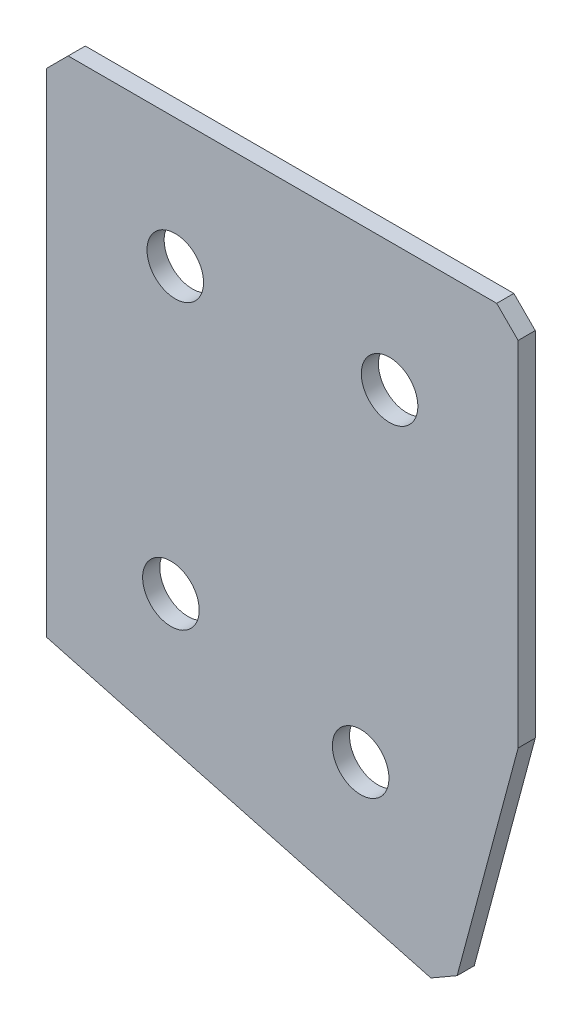
SolidWorks part; units mm, degrees
material "Простая углеродистая сталь"
ref_plane "Спереди" through (0, 0, 0) normal (0, 0, 1) x (1, 0, 0)
ref_plane "Сверху" through (0, 0, 0) normal (0, 1, 0) x (1, 0, 0)
ref_plane "Справа" through (0, 0, 0) normal (1, 0, 0) x (0, 0, -1)
sketch "Эскиз3" plane through (0, 0, 0) normal (0, 0, -1) x (1, 0, 0)
  line L0 (0, 0) -> (55, 0)
  line L1 (55, 0) -> (55, 43.6789)
  line L2 (0, 0) -> (0, 60)
  line L3 (0, 60) -> (47.2354, 72.6567)
  line L4 (47.2354, 72.6567) -> (55, 43.6789)
  dimension "D1" = 55
  dimension "D2" = 60
  dimension "D3" = 30
  dimension "D4" = 15
  dimension "D5" = 43.6789
extrude "Бобышка-Вытянуть1" add sketch "Эскиз3" along normal blind 2
hole_wizard "Отверстие с зазором M61" positions "Эскиз4" profile "Эскиз5" hole size "M6" standard "DIN" end condition through all
sketch "Эскиз4" plane through (0, 0, -2) normal (0, 0, -1) x (1, 0, 0)
  line L0 (14.4889, 48.3531) -> (36.6288, 54.2855) construction
  line L2 (47.2354, 72.6567) -> (0, 60) construction
  line L3 (15, 15) -> (40, 15) construction
  line L5 (0, 0) -> (55, 0) construction
  line L6 (0, 60) -> (0, 0) construction
  line L7 (55, 0) -> (55, 43.6789) construction
  line L8 (55, 43.6789) -> (47.2354, 72.6567) construction
  line L9 (14.4889, 48.3531) -> (0, 44.4709) construction
  point P0 (15, 15)
  point P2 (40, 15)
  point P4 (14.4889, 48.3531)
  point P6 (36.6288, 54.2855)
  dimension "D1" = 15
  dimension "D2" = 15
  dimension "D3" = 15
  dimension "D4" = 15
  dimension "D5" = 15
  dimension "D6" = 15
  dimension "D7" = 22.921
  dimension "D8" = 25
sketch "Эскиз5" plane through (15, -15, -2) normal (1, 0, 0) x (0, 1, 0)
  line L0 (0, 0) -> (0, 2)
  line L1 (0, 2) -> (3.3, 2)
  line L2 (3.3, 2) -> (3.3, 0)
  line L5 (3.3, 0) -> (0, 0)
  line L11 (0, -6.35) -> (0, 107.95) construction
  dimension "Диаметр сквозного отверстия" = 6.6
  dimension "Глубина сквозного отверстия" = 2
chamfer "Фаска1" distance 2.5 distance2 2.5 3 edges at (47.2354, -72.6567, -1) (55, 0, -1) (0, 0, -1)
